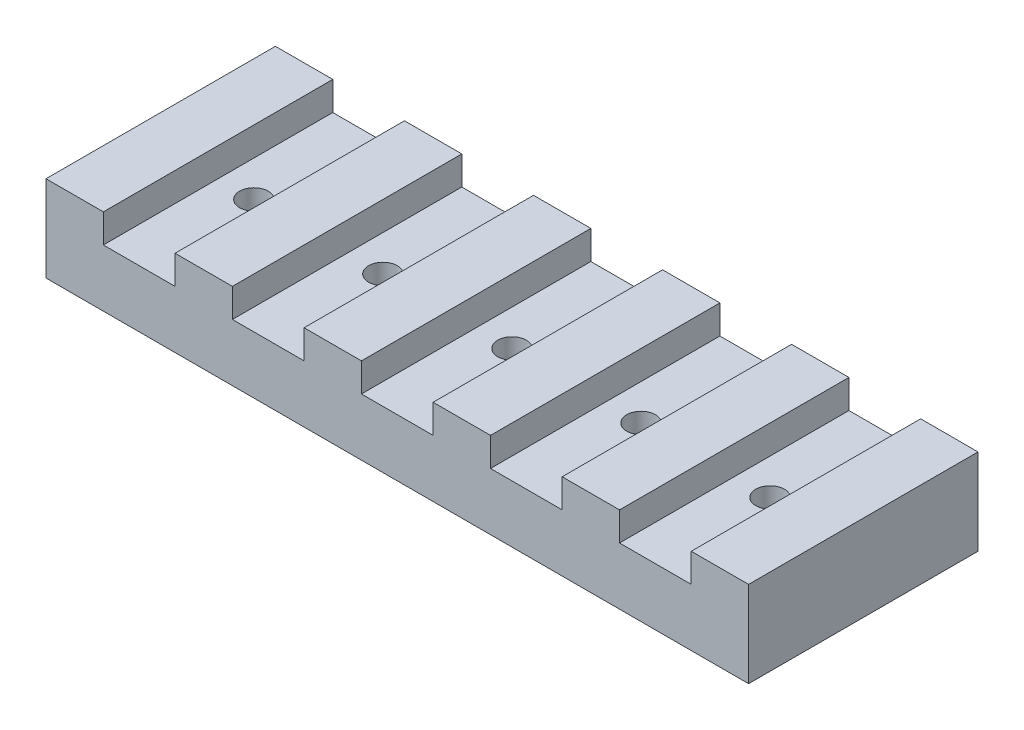
SolidWorks part; units mm, degrees
ref_plane "Front Plane" through (0, 0, 0) normal (0, 0, 1) x (1, 0, 0)
ref_plane "Top Plane" through (0, 0, 0) normal (0, 1, 0) x (1, 0, 0)
ref_plane "Right Plane" through (0, 0, 0) normal (1, 0, 0) x (0, 0, -1)
sketch "Sketch1" plane through (0, 0, 0) normal (0, 0, 1) x (1, 0, 0)
  line L0 (-65.0875, 12.7) -> (-49.2125, 12.7) construction
  line L1 (-77.7875, -6.35) -> (77.7875, -6.35)
  line L2 (-77.7875, -6.35) -> (-77.7875, 6.35)
  line L3 (-77.7875, 6.35) -> (77.7875, 6.35)
  line L4 (77.7875, -6.35) -> (77.7875, 6.35)
  line L5 (-77.7875, -6.35) -> (77.7875, 6.35) construction
  line L6 (-77.7875, 6.35) -> (77.7875, -6.35) construction
  line L7 (-77.7875, 6.35) -> (-65.0875, 6.35)
  line L8 (-77.7875, 6.35) -> (-77.7875, 12.7)
  line L9 (-77.7875, 12.7) -> (-65.0875, 12.7)
  line L10 (-65.0875, 6.35) -> (-65.0875, 12.7)
  line L11 (-49.2125, 6.35) -> (-36.5125, 6.35)
  line L12 (-49.2125, 6.35) -> (-49.2125, 12.7)
  line L13 (-49.2125, 12.7) -> (-36.5125, 12.7)
  line L14 (-36.5125, 6.35) -> (-36.5125, 12.7)
  line L15 (-20.6375, 6.35) -> (-7.9375, 6.35)
  line L16 (-20.6375, 6.35) -> (-20.6375, 12.7)
  line L17 (-20.6375, 12.7) -> (-7.9375, 12.7)
  line L18 (-7.9375, 6.35) -> (-7.9375, 12.7)
  line L19 (77.7875, 6.35) -> (65.0875, 6.35)
  line L20 (77.7875, 6.35) -> (77.7875, 12.7)
  line L21 (77.7875, 12.7) -> (65.0875, 12.7)
  line L22 (65.0875, 6.35) -> (65.0875, 12.7)
  line L23 (36.5125, 6.35) -> (49.2125, 6.35)
  line L24 (36.5125, 6.35) -> (36.5125, 12.7)
  line L25 (36.5125, 12.7) -> (49.2125, 12.7)
  line L26 (49.2125, 6.35) -> (49.2125, 12.7)
  line L27 (7.9375, 6.35) -> (20.6375, 6.35)
  line L28 (7.9375, 6.35) -> (7.9375, 12.7)
  line L29 (7.9375, 12.7) -> (20.6375, 12.7)
  line L30 (20.6375, 6.35) -> (20.6375, 12.7)
  line L31 (-36.5125, 12.7) -> (-20.6375, 12.7) construction
  line L32 (-7.9375, 12.7) -> (7.9375, 12.7) construction
  line L33 (20.6375, 12.7) -> (36.5125, 12.7) construction
  line L34 (49.2125, 12.7) -> (65.0875, 12.7) construction
  point P0 (0, 0)
  dimension "D1" = 15.875
  dimension "D2" = 12.7
  dimension "D3" = 6.35
  dimension "D4" = 12.7
extrude "Boss-Extrude1" add sketch "Sketch1" along normal mid plane 50.8 contours L1 L4 L3 L2 | L22 L3 L20 L21 | L3 L26 L25 L24 | L3 L30 L29 L28 | L3 L18 L17 L16 | L3 L10 L9 L8 | L3 L14 L13 L12
sketch "Sketch2" plane through (0, 6.35, 0) normal (0, 1, 0) x (1, 0, 0)
  line L0 (-57.15, 0) -> (-28.575, 0) construction
  line L1 (-28.575, 0) -> (0, 0) construction
  line L2 (-65.0875, 25.4) -> (-49.2125, -25.4) construction
  circle A0 centre (0, 0) radius 3.175
  circle A1 centre (-28.575, 0) radius 3.175
  circle A2 centre (-57.15, 0) radius 3.175
  point P9 (-57.15, 0)
  dimension "D1" = 6.35
extrude "Cut-Extrude1" cut sketch "Sketch2" against normal through all
mirror "Mirror1" about plane through (0, 0, 0) normal (1, 0, 0) of "Cut-Extrude1"
